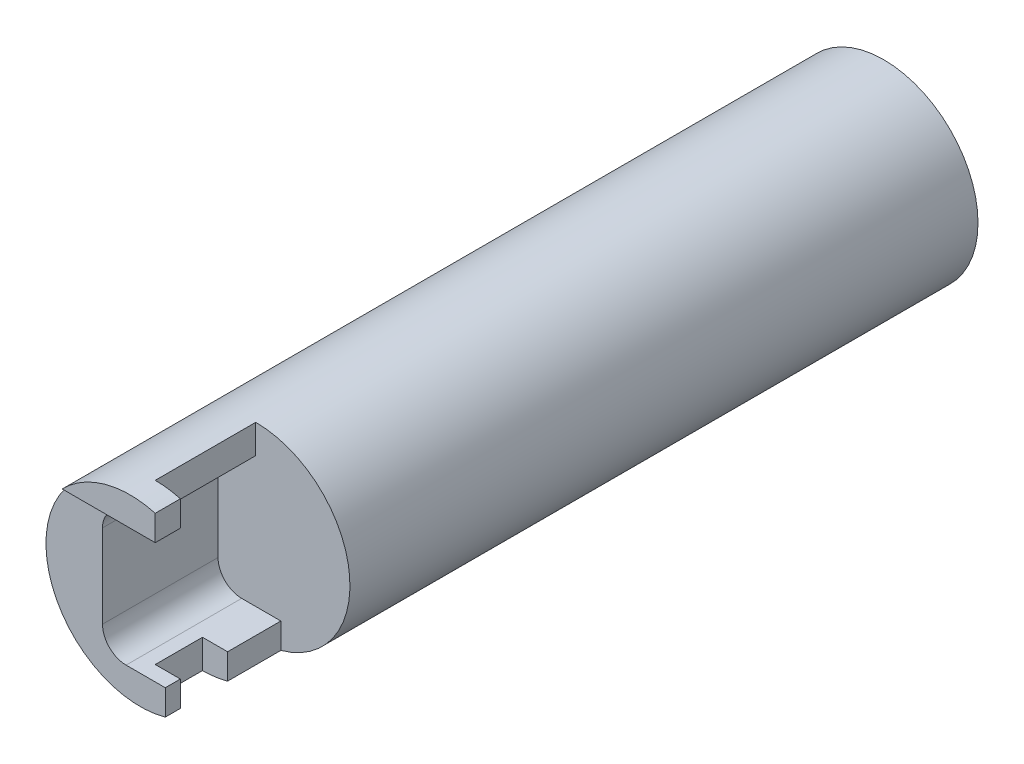
SolidWorks part; units mm, degrees
ref_plane "Front" through (0, 0, 0) normal (0, 0, 1) x (1, 0, 0)
ref_plane "Top" through (0, 0, 0) normal (0, 1, 0) x (1, 0, 0)
ref_plane "Right" through (0, 0, 0) normal (1, 0, 0) x (0, 0, -1)
sketch "Sketch1" plane through (0, 0, 0) normal (0, 0, 1) x (1, 0, 0)
  circle A0 centre (0, 0) radius 4.7625
  dimension "D1" = 9.525
extrude "Extrude1" add sketch "Sketch1" along normal blind 38.1
sketch "Sketch3" plane through (0, 0, 38.1) normal (0, 0, 1) x (1, 0, 0)
  circle A0 centre (0, 0) radius 5.08
  circle A1 centre (0, 0) radius 4.7625 construction
  circle A2 centre (0, 0) radius 4.7625
  dimension "D1" = 10.16
extrude "Extrude3" [suppressed] cut sketch "Sketch3" against normal blind 6.35
sketch "Sketch2" plane through (0, 0, 38.1) normal (0, 0, 1) x (1, 0, 0)
  line L0 (-18.4523, 0) -> (19.8802, 0) construction
  line L1 (-0.7112, 3.302) -> (1.27, 3.302)
  line L3 (-0.7112, -3.302) -> (1.27, -3.302)
  line L4 (23.8096, 10.556) -> (23.8096, -10.556)
  line L7 (1.27, 3.302) -> (1.27, 10.556)
  line L8 (1.27, 10.556) -> (23.8096, 10.556)
  line L9 (1.27, -3.302) -> (1.27, -10.556)
  line L10 (1.27, -10.556) -> (23.8096, -10.556)
  line L11 (-1.905, -2.1082) -> (-1.905, 2.1082)
  line L13 (0, 0) -> (0, 12.4475) construction
  arc A0 (-1.905, -2.1082) -> (-0.7112, -3.302) centre (-0.7112, -2.1082) ccw
  arc A1 (-1.905, 2.1082) -> (-0.7112, 3.302) centre (-0.7112, 2.1082) cw
  dimension "D4" = 1.1938
  dimension "D1" = 6.604
  dimension "D2" = 1.905
  dimension "D3" = 1.27
extrude "Extrude2" cut sketch "Sketch2" against normal blind 6.35
sketch "Sketch4" plane through (0, 0, 38.1) normal (0, 0, 1) x (1, 0, 0)
  line L1 (-6.2579, -6.8061) -> (5.7366, -6.8061)
  line L2 (-6.2579, -6.8061) -> (-6.2579, 3.302)
  line L3 (-6.2579, 3.302) -> (5.7366, 3.302)
  line L4 (5.7366, -6.8061) -> (5.7366, 3.302)
  line L5 (1.27, 3.302) -> (-0.7112, 3.302) construction
extrude "Extrude4" cut sketch "Sketch4" against normal blind 0.508
sketch "Sketch5" plane through (1.27, 0, 0) normal (1, 0, 0) x (0, 0, -1)
  line L0 (-37.592, -3.302) -> (-37.592, -4.59) construction
  line L2 (-36.83, 5.9026) -> (-36.83, -11.4577)
  line L3 (-36.83, -11.4577) -> (-34.4424, -11.4577)
  line L4 (-34.4424, 3.302) -> (-34.4424, -11.4577)
  line L5 (-31.75, 4.59) -> (-31.75, 3.302) construction
  line L6 (-31.75, 3.302) -> (-38.1, 3.302) construction
  line L8 (-31.75, 5.9026) -> (-31.75, 3.302)
  line L9 (-31.75, 3.302) -> (-34.4424, 3.302)
  line L10 (-36.83, 5.9026) -> (-31.75, 5.9026)
  dimension "D1" = 2.3876
  dimension "D2" = 0.762
extrude "Extrude5" cut sketch "Sketch5" against normal blind 1.27
